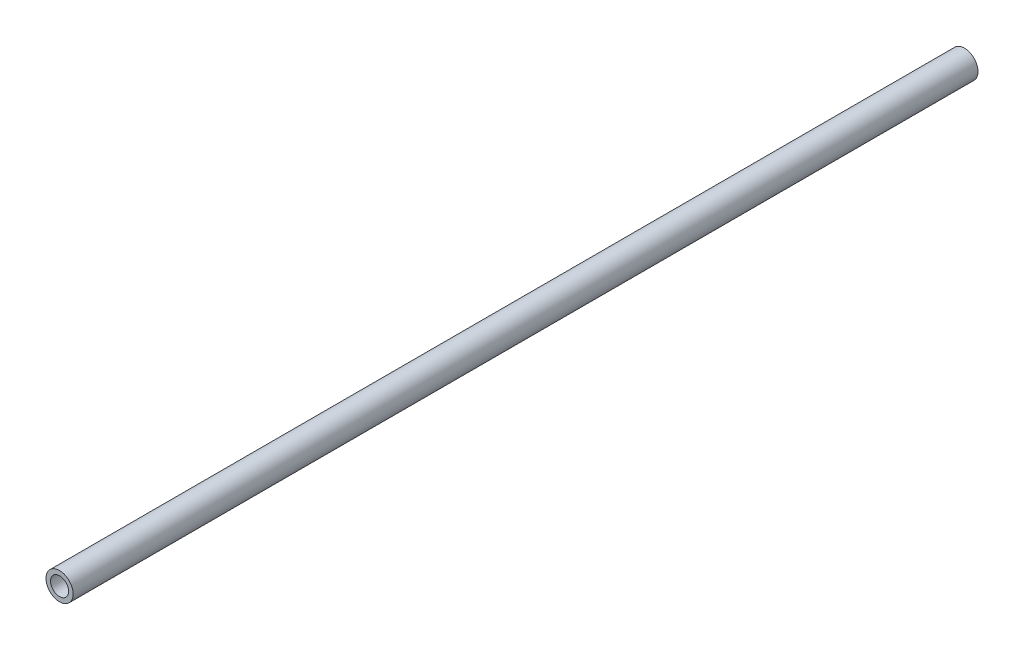
SolidWorks part; units mm, degrees
ref_plane "Front Plane" through (0, 0, 0) normal (0, 0, 1) x (1, 0, 0)
ref_plane "Top Plane" through (0, 0, 0) normal (0, 1, 0) x (1, 0, 0)
ref_plane "Right Plane" through (0, 0, 0) normal (1, 0, 0) x (0, 0, -1)
sketch "Sketch1" plane through (0, 0, 0) normal (0, 0, 1) x (1, 0, 0)
  circle A0 centre (0, 0) radius 10
  circle A1 centre (0, 0) radius 15
extrude "Boss-Extrude1" add sketch "Sketch1" along normal blind 1000 contours A1 | A0
